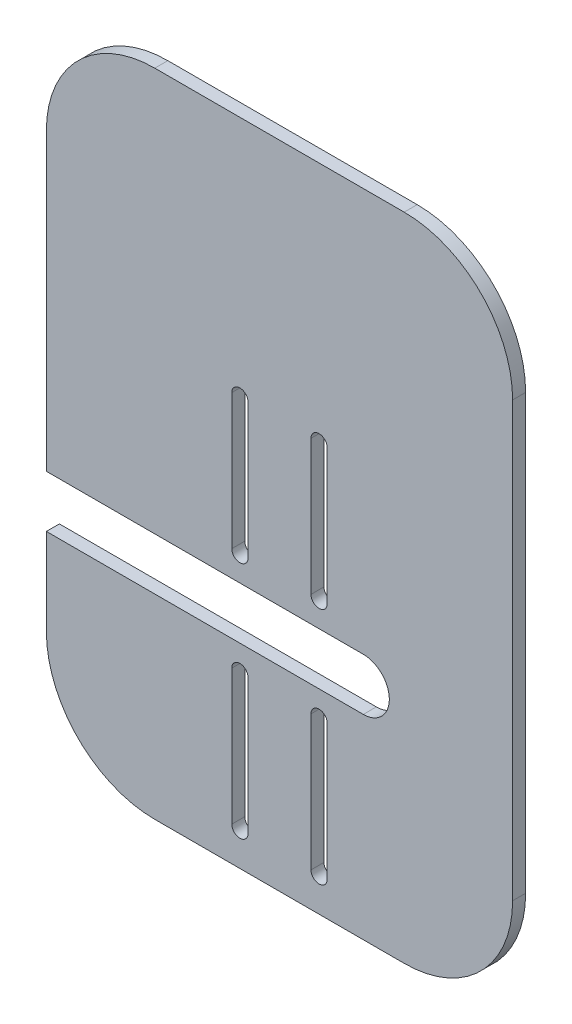
SolidWorks part; units mm, degrees
ref_plane "Front Plane" through (0, 0, 0) normal (0, 0, 1) x (1, 0, 0)
ref_plane "Top Plane" through (0, 0, 0) normal (0, 1, 0) x (1, 0, 0)
ref_plane "Right Plane" through (0, 0, 0) normal (1, 0, 0) x (0, 0, -1)
sketch "Sketch2" plane through (0, 0, 0) normal (0, 0, 1) x (1, 0, 0)
  line L0 (-66.4419, -25.5476) -> (-31.1286, -25.5476) construction
  line L1 (-53.1286, -19.5476) -> (-62.7468, -19.5476)
  line L2 (-53.1286, -31.5476) -> (-62.7468, -31.5476)
  line L3 (-72.4536, -25.5476) -> (-72.4536, 195.4577) construction
  line L4 (-72.4536, -25.5476) -> (-72.4536, -76.5476) construction
  line L5 (-72.4536, 195.4577) -> (-72.4536, 73.4524) construction
  line L6 (-101.2036, 73.4524) -> (-43.7036, 73.4524)
  line L7 (-126.2036, 48.4524) -> (-126.2036, -19.5476)
  line L8 (-101.2036, -76.5476) -> (-43.7036, -76.5476)
  line L9 (-18.7036, 48.4524) -> (-18.7036, -51.5476)
  line L10 (-62.7468, -19.5476) -> (-126.2036, -19.5476)
  line L11 (-62.7468, -31.5476) -> (-126.2036, -31.5476)
  line L12 (-126.2036, -31.5476) -> (-126.2036, -51.5476)
  arc A1 (-53.1286, -31.5476) -> (-53.1286, -19.5476) centre (-53.1286, -25.5476) ccw
  arc A2 (-101.2036, 73.4524) -> (-126.2036, 48.4524) centre (-101.2036, 48.4524) ccw
  arc A3 (-43.7036, 73.4524) -> (-18.7036, 48.4524) centre (-43.7036, 48.4524) cw
  arc A4 (-18.7036, -51.5476) -> (-43.7036, -76.5476) centre (-43.7036, -51.5476) cw
  arc A5 (-101.2036, -76.5476) -> (-126.2036, -51.5476) centre (-101.2036, -51.5476) cw
  dimension "D1" = 45
  dimension "D2" = 12
  dimension "D4" = 25
  dimension "D3" = 22
  dimension "D5" = 150
  dimension "D6" = 107.5
extrude "Boss-Extrude1" add sketch "Sketch2" along normal blind 3
sketch "Sketch3" plane through (0, 0, 3) normal (0, 0, 1) x (1, 0, 0)
  line L0 (-72.4536, 73.4524) -> (-72.4536, -76.5476) construction
  line L1 (-43.7036, 73.4524) -> (-101.2036, 73.4524) construction
  line L2 (-101.2036, -76.5476) -> (-43.7036, -76.5476) construction
  line L3 (-47.1286, -25.5476) -> (-126.2036, -25.5476) construction
  line L4 (-63.3236, -37.4766) -> (-63.3236, -68.6318) construction
  line L5 (-61.4486, -37.4766) -> (-61.4486, -68.6318)
  line L6 (-65.1986, -37.4766) -> (-65.1986, -68.6318)
  line L7 (-81.5836, -37.4766) -> (-81.5836, -68.6318) construction
  line L8 (-83.4586, -37.4766) -> (-83.4586, -68.6318)
  line L9 (-79.7086, -37.4766) -> (-79.7086, -68.6318)
  line L10 (-81.5836, -13.6186) -> (-81.5836, 17.5367) construction
  line L11 (-83.4586, -13.6186) -> (-83.4586, 17.5367)
  line L12 (-79.7086, -13.6186) -> (-79.7086, 17.5367)
  line L13 (-63.3236, -13.6186) -> (-63.3236, 17.5367) construction
  line L14 (-61.4486, -13.6186) -> (-61.4486, 17.5367)
  line L15 (-65.1986, -13.6186) -> (-65.1986, 17.5367)
  arc A0 (-53.1286, -31.5476) -> (-53.1286, -19.5476) centre (-53.1286, -25.5476) ccw construction
  arc A1 (-61.4486, -37.4766) -> (-65.1986, -37.4766) centre (-63.3236, -37.4766) ccw
  arc A2 (-65.1986, -68.6318) -> (-61.4486, -68.6318) centre (-63.3236, -68.6318) ccw
  arc A3 (-83.4586, -37.4766) -> (-79.7086, -37.4766) centre (-81.5836, -37.4766) cw
  arc A4 (-79.7086, -68.6318) -> (-83.4586, -68.6318) centre (-81.5836, -68.6318) cw
  arc A5 (-83.4586, -13.6186) -> (-79.7086, -13.6186) centre (-81.5836, -13.6186) ccw
  arc A6 (-79.7086, 17.5367) -> (-83.4586, 17.5367) centre (-81.5836, 17.5367) ccw
  arc A7 (-61.4486, -13.6186) -> (-65.1986, -13.6186) centre (-63.3236, -13.6186) cw
  arc A8 (-65.1986, 17.5367) -> (-61.4486, 17.5367) centre (-63.3236, 17.5367) cw
  point P14 (-63.3236, -53.0542)
  point P21 (-81.5836, -53.0542)
  point P28 (-81.5836, 1.959)
  point P35 (-63.3236, 1.959)
  dimension "D3" = 1.875
  dimension "D1" = 3.75
  dimension "D2" = 9.13
extrude "Cut-Extrude1" cut sketch "Sketch3" against normal blind 10
